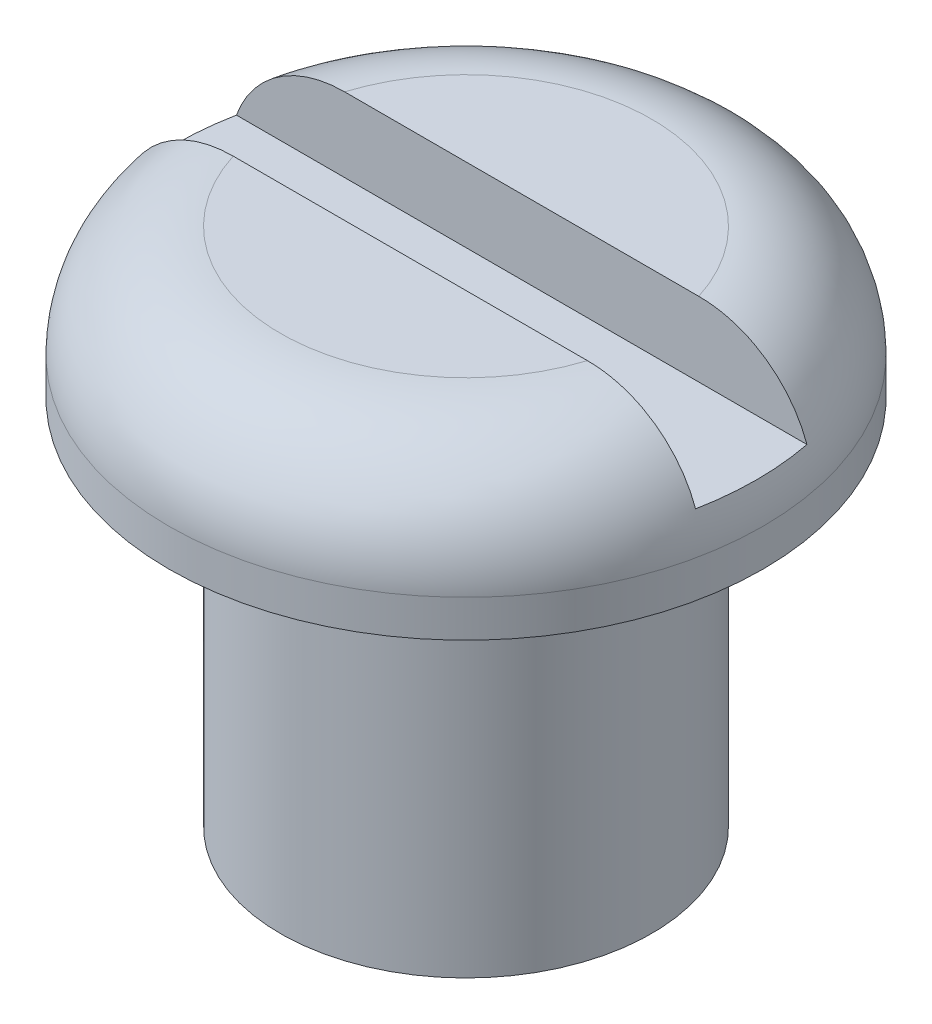
SolidWorks part; units mm, degrees
ref_plane "Plano frontal" through (0, 0, 0) normal (0, 0, 1) x (1, 0, 0)
ref_plane "Plano superior" through (0, 0, 0) normal (0, 1, 0) x (1, 0, 0)
ref_plane "Plano direito" through (0, 0, 0) normal (1, 0, 0) x (0, 0, -1)
sketch "Esboço1" plane through (0, 0, 0) normal (0, 0, 1) x (1, 0, 0)
  line L0 (0, 0) -> (2.5, 0)
  line L1 (2.5, 0) -> (2.5, 5)
  line L2 (2.5, 5) -> (4, 5)
  line L3 (4, 5) -> (4, 5.5)
  line L4 (0, 7) -> (0, 0) construction
  line L5 (0, 7) -> (2.5, 7)
  line L6 (0, 0) -> (0, 7)
  arc A0 (4, 5.5) -> (2.5, 7) centre (2.5, 5.5) ccw
  dimension "D1" = 5
  dimension "D2" = 8
  dimension "D3" = 2
  dimension "D4" = 5
  dimension "D5" = 5
revolve "Revolução1" add sketch "Esboço1" angle 360 about L4
sketch "Esboço2" plane through (0, 0, 0) normal (0, 0, 1) x (1, 0, 0)
  line L1 (2.5, 7) -> (-2.5, 7) construction
  line L2 (4, 6) -> (-4, 6)
  line L3 (4, 6) -> (4, 7)
  line L4 (4, 7) -> (-4, 7)
  line L5 (-4, 6) -> (-4, 7)
  line L6 (-4, 5.5) -> (-4, 5) construction
  dimension "D1" = 1
  dimension "D2" = 8
extrude "Corte-extrusão1" cut sketch "Esboço2" against normal mid plane 1.5
